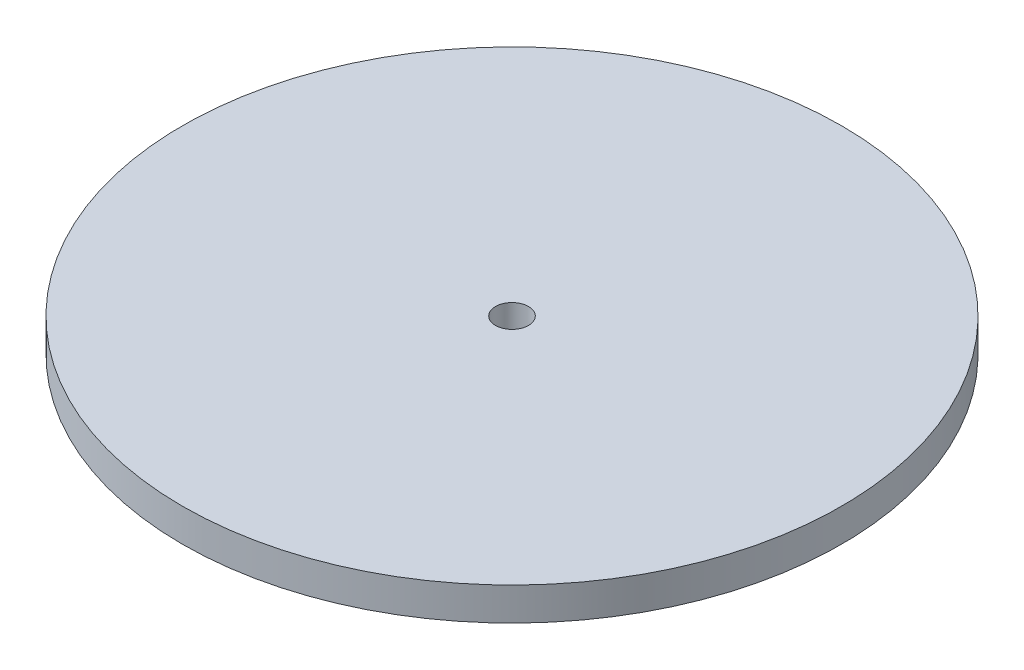
SolidWorks part; units mm, degrees
ref_plane "Front Plane" through (0, 0, 0) normal (0, 0, 1) x (1, 0, 0)
ref_plane "Top Plane" through (0, 0, 0) normal (0, 1, 0) x (1, 0, 0)
ref_plane "Right Plane" through (0, 0, 0) normal (1, 0, 0) x (0, 0, -1)
sketch "Sketch1" plane through (0, 0, 0) normal (0, 1, 0) x (1, 0, 0)
  circle A0 centre (0, 0) radius 63.5
  dimension "D1" = 127
extrude "Boss-Extrude1" add sketch "Sketch1" along normal blind 6.35
hole_wizard "1/4 (0.25) Diameter Hole1" positions "Sketch3" profile "Sketch2" hole size "1/4" standard "ANSI Inch" end condition through all
sketch "Sketch3" plane through (0, 0, 0) normal (0, -1, 0) x (-1, 0, 0)
  point P0 (0, 0)
sketch "Sketch2" plane through (0, 0, 0) normal (1, 0, 0) x (0, 0, -1)
  line L0 (0, 0) -> (0, 6.35)
  line L1 (0, 6.35) -> (3.175, 6.35)
  line L2 (3.175, 6.35) -> (3.175, 0)
  line L5 (3.175, 0) -> (0, 0)
  line L11 (0, -6.35) -> (0, 107.95) construction
  dimension "Thru Hole Dia." = 6.35
  dimension "Thru Hole Depth" = 6.35
